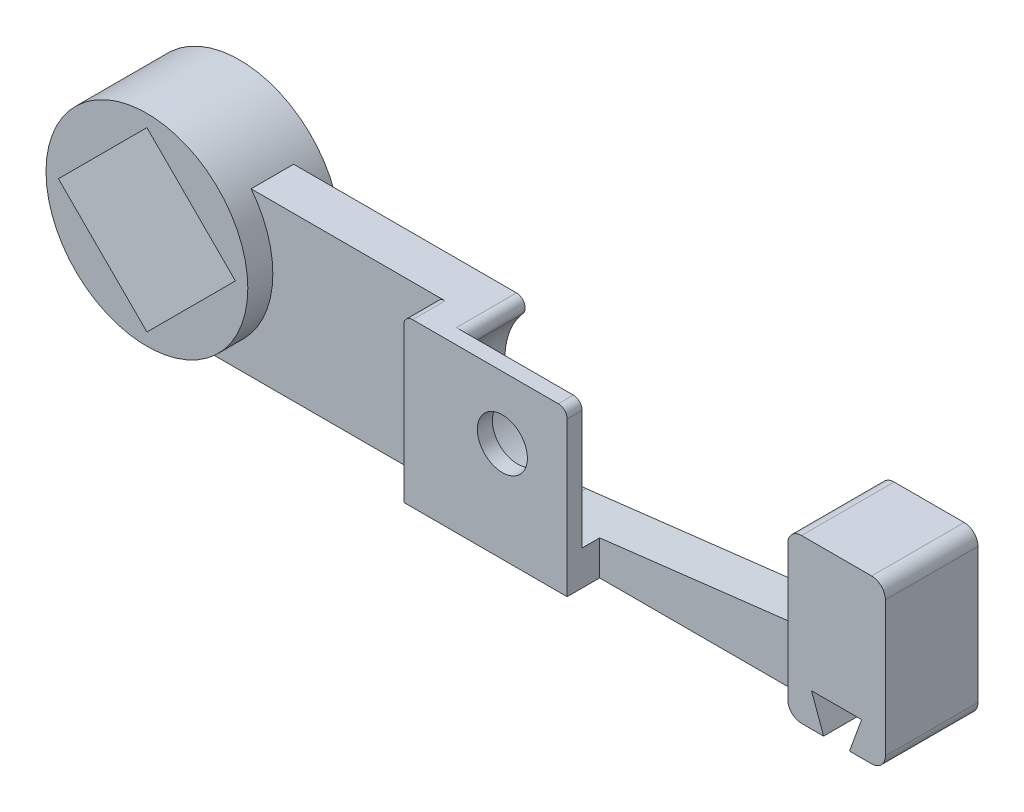
SolidWorks part; units mm, degrees
ref_plane "Front Plane" through (0, 0, 0) normal (0, 0, 1) x (1, 0, 0)
ref_plane "Top Plane" through (0, 0, 0) normal (0, 1, 0) x (1, 0, 0)
ref_plane "Right Plane" through (0, 0, 0) normal (1, 0, 0) x (0, 0, -1)
sketch "Sketch1" plane through (0, 0, 0) normal (0, 1, 0) x (1, 0, 0)
  line L1 (-19.05, -1.0795) -> (19.05, -1.0795)
  line L2 (-19.05, -1.0795) -> (-19.05, 1.0795)
  line L3 (-19.05, 1.0795) -> (19.05, 1.0795)
  line L4 (19.05, -1.0795) -> (19.05, 1.0795)
  line L5 (-19.05, -1.0795) -> (19.05, 1.0795) construction
  line L6 (-19.05, 1.0795) -> (19.05, -1.0795) construction
  point P0 (0, 0)
  dimension "D1" = 2.159
  dimension "D2" = 38.1
extrude "Boss-Extrude1" add sketch "Sketch1" along normal blind 8.255
sketch "Sketch2" plane through (0, 0, 1.0795) normal (0, 0, 1) x (1, 0, 0)
  line L0 (0, 8.255) -> (0, 0) construction
  line L1 (-19.05, 8.255) -> (19.05, 8.255) construction
  line L2 (0, 5.08) -> (14.097, 5.08) construction
  line L3 (0.4351, 8.7372) -> (14.097, 7.112) construction
  line L4 (14.097, 5.08) -> (14.097, 7.112) construction
  line L5 (15.9016, 5.08) -> (14.097, 5.08) construction
  line L6 (0.4351, 1.4228) -> (14.097, 3.048)
  line L8 (0, 8.763) -> (-0.4351, 13.4106)
  line L9 (14.097, 7.112) -> (14.8394, 13.3525)
  line L11 (0.4351, 13.4106) -> (14.8394, 13.3525)
  line L14 (-0.4351, 13.4106) -> (0.4351, 13.4106)
  circle A0 centre (0, 5.08) radius 3.683 construction
  arc A1 (14.097, 7.112) -> (14.097, 3.048) centre (13.8553, 5.08) cw
  arc A3 (-0.4351, 1.4228) -> (0.4351, 1.4228) centre (0, 5.08) ccw
  arc A4 (-0.4351, 1.4228) -> (0, 8.763) centre (0, 5.08) cw
  dimension "D1" = 7.366
  dimension "D2" = 14.097
  dimension "D3" = 2.032
  dimension "D4" = 3.175
extrude "Cut-Extrude1" cut sketch "Sketch2" against normal blind 12.7
fillet "Fillet5" radius 0.4826 2 edges at (14.233, 8.255, 0) (14.097, 7.112, 0)
fillet "Fillet7" radius 0.4445 1 edges at (-1.8665, 8.255, 0)
sketch "Sketch3" plane through (0, 0, 1.0795) normal (0, 0, 1) x (1, 0, 0)
  line L2 (-19.05, 0) -> (19.05, 0) construction
  line L7 (19.05, 8.255) -> (14.097, 8.255)
  line L8 (19.05, 8.255) -> (19.05, 0)
  line L9 (19.05, 0) -> (14.097, 0)
  line L10 (14.097, 8.255) -> (14.097, 0)
  dimension "D1" = 4.953
extrude "Boss-Extrude2" add sketch "Sketch3" along normal blind 1.27
ref_plane "Plane1" through (0, 0, 0) normal (0, 0, 1) x (1, 0, 0)
mirror "Mirror2" about plane through (0, 0, 0) normal (0, 0, 1) of "Boss-Extrude2"
sketch "Sketch8" plane through (0, 0, 2.3495) normal (0, 0, 1) x (1, 0, 0)
  line L0 (16.5735, 0) -> (16.5735, 1.6891) construction
  line L1 (15.3035, 1.6891) -> (17.8435, 1.6891)
  line L2 (17.8435, 1.6891) -> (17.2287, 0)
  line L3 (15.3035, 1.6891) -> (15.9183, 0)
  line L4 (17.2287, 0) -> (15.9183, 0)
  line L5 (16.5735, 0) -> (16.5735, 2.7272) construction
  line L6 (14.097, 0) -> (19.05, 0) construction
  point P4 (16.5735, 1.6891)
  point P11 (0, 0)
  dimension "D1" = 1.6891
  dimension "D2" = 2.54
  dimension "D3" = 70
  dimension "D4" = 70
extrude "Cut-Extrude4" cut sketch "Sketch8" against normal through all
fillet "Fillet9" radius 0.6985 5 edges at (14.097, 0, -1.7145) (14.097, 0, 1.7145) (14.097, 8.255, -1.7145) (19.05, 0, 0) (19.05, 8.255, 0)
sketch "Sketch4" plane through (0, 0, 2.3495) normal (0, 0, 1) x (1, 0, 0)
  line L7 (0, 5.08) -> (-18.415, 5.08) construction
  line L9 (-20.6601, 7.3251) -> (-18.415, 9.5701) construction
  line L10 (-20.6601, 2.8349) -> (-16.1699, 2.8349) construction
  line L11 (-20.6601, 2.8349) -> (-20.6601, 7.3251) construction
  line L12 (-20.6601, 7.3251) -> (-16.1699, 7.3251) construction
  line L13 (-16.1699, 2.8349) -> (-16.1699, 7.3251) construction
  line L14 (-20.6601, 2.8349) -> (-16.1699, 7.3251) construction
  line L15 (-20.6601, 7.3251) -> (-16.1699, 2.8349) construction
  line L16 (-18.415, 9.5701) -> (-16.1699, 7.3251) construction
  line L17 (-18.415, 0.5899) -> (-22.9051, 5.08)
  line L18 (-18.415, 0.5899) -> (-13.9249, 5.08)
  line L19 (-22.9051, 5.08) -> (-18.415, 9.5701)
  line L20 (-13.9249, 5.08) -> (-18.415, 9.5701)
  line L21 (-18.415, 0.5899) -> (-18.415, 9.5701) construction
  line L22 (-22.9051, 5.08) -> (-13.9249, 5.08) construction
  circle A0 centre (-18.415, 5.08) radius 5.1195
  point P0 (-19.05, 5.08)
  dimension "D8" = 6.35
  dimension "D1" = 18.415
  dimension "D6" = 6.35
  dimension "D7" = 90
extrude "Boss-Extrude3" add sketch "Sketch4" against normal up to surface (4.699 mm away) up to face at (16.5735, 3.0332, -2.3495)
sketch "Sketch7" plane through (0, 0, 2.3495) normal (0, 0, 1) x (1, 0, 0)
  line L16 (-22.9051, 5.08) -> (-18.415, 9.5701)
  line L17 (-22.9051, 5.08) -> (-18.415, 0.5899)
  line L18 (-18.415, 9.5701) -> (-13.9249, 5.08)
  line L19 (-18.415, 0.5899) -> (-13.9249, 5.08)
  line L20 (-13.9249, 5.08) -> (-18.415, 0.5899) construction
extrude "Cut-Extrude3" cut sketch "Sketch7" against normal up to surface (4.699 mm away) up to face at (-13.2955, 5.08, -2.3495)
sketch "Sketch9" plane through (0, 0, 1.0795) normal (0, 0, 1) x (1, 0, 0)
  line L0 (0.4351, 1.4228) -> (14.097, 3.048) construction
  line L1 (-3.0953, 8.255) -> (-5.0003, 8.255)
  line L2 (-14.3989, 8.255) -> (-3.0953, 8.255) construction
  line L3 (-5.0003, 8.255) -> (-5.0003, 0)
  line L4 (-17.78, 0) -> (14.7955, 0) construction
  line L5 (-5.0003, 0) -> (0.1104, 0)
  line L7 (0.4351, 1.4228) -> (3.2854, 1.7619)
  line L8 (3.2854, 1.7619) -> (3.2854, 0)
  line L9 (3.2854, 0) -> (0.1104, 0)
  arc A0 (-2.7619, 7.5164) -> (0.4351, 1.4228) centre (0, 5.08) ccw
  arc A1 (-2.7619, 7.5164) -> (-3.0953, 8.255) centre (-3.0953, 7.8105) ccw
  dimension "D1" = 1.905
  dimension "D2" = 3.175
extrude "Boss-Extrude4" add sketch "Sketch9" along normal blind 0.889
sketch "Sketch10" plane through (0, 0, 1.9685) normal (0, 0, 1) x (1, 0, 0)
  line L0 (3.2854, 0) -> (-5.0003, 0)
  line L1 (3.2854, 0) -> (3.2854, 8.255)
  line L2 (-5.0003, 0) -> (-5.0003, 8.255)
  line L3 (3.2854, 8.255) -> (-5.0003, 8.255)
  line L4 (-3.0953, 8.255) -> (-5.0003, 8.255) construction
extrude "Boss-Extrude5" add sketch "Sketch10" along normal blind 0.762
fillet "Fillet10" radius 0.4445 2 edges at (-5.0003, 8.255, 1.905) (3.2854, 8.255, 2.3495)
sketch "Sketch11" plane through (0, 0, 1.9685) normal (0, 0, -1) x (-1, 0, 0)
  circle A1 centre (0, 5.08) radius 1.27
  dimension "D1" = 2.54
extrude "Cut-Extrude5" cut sketch "Sketch11" against normal through all
